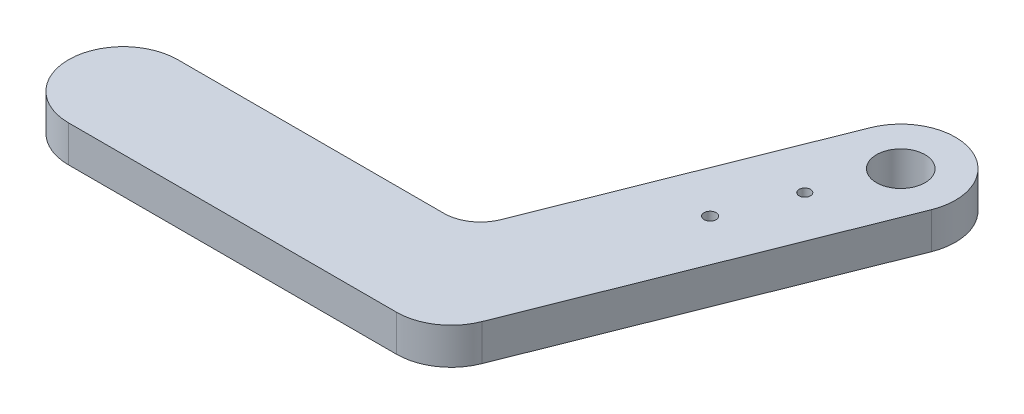
SolidWorks part; units mm, degrees
ref_plane "Front Plane" through (0, 0, 0) normal (0, 0, 1) x (1, 0, 0)
ref_plane "Top Plane" through (0, 0, 0) normal (0, 1, 0) x (1, 0, 0)
ref_plane "Right Plane" through (0, 0, 0) normal (1, 0, 0) x (0, 0, -1)
sketch "Sketch1" plane through (0, 0, 0) normal (0, 1, 0) x (1, 0, 0)
  line L1 (6.082, -5.3683) -> (16.6071, 21.1171) construction
  line L3 (20.789, 19.4552) -> (10.2639, -7.0301)
  line L4 (12.4252, 22.7789) -> (3.7798, 1.0238)
  line L5 (0.9919, -0.8683) -> (-20.918, -0.8683)
  line L6 (-20.918, -9.8683) -> (6.082, -9.8683)
  line L7 (16.6071, 21.1171) -> (6.082, -5.3683) construction
  line L9 (-20.918, -5.3683) -> (6.082, -5.3683) construction
  arc A3 (3.7798, 1.0238) -> (0.9919, -0.8683) centre (0.9919, 2.1317) cw
  arc A4 (12.4252, 22.7789) -> (20.789, 19.4552) centre (16.6071, 21.1171) cw
  arc A5 (10.2639, -7.0301) -> (6.082, -9.8683) centre (6.082, -5.3683) cw
  arc A6 (-20.918, -0.8683) -> (-20.918, -9.8683) centre (-20.918, -5.3683) ccw
  circle A7 centre (16.6071, 21.1171) radius 2
  circle A8 centre (12.1441, 9.8863) radius 0.5
  circle A9 centre (14.3599, 15.4622) radius 0.4676
  dimension "D5" = 12.085
  dimension "D1" = 9
  dimension "D3" = 6
  dimension "D2" = 9
extrude "Boss-Extrude1" add sketch "Sketch1" along normal blind 3
